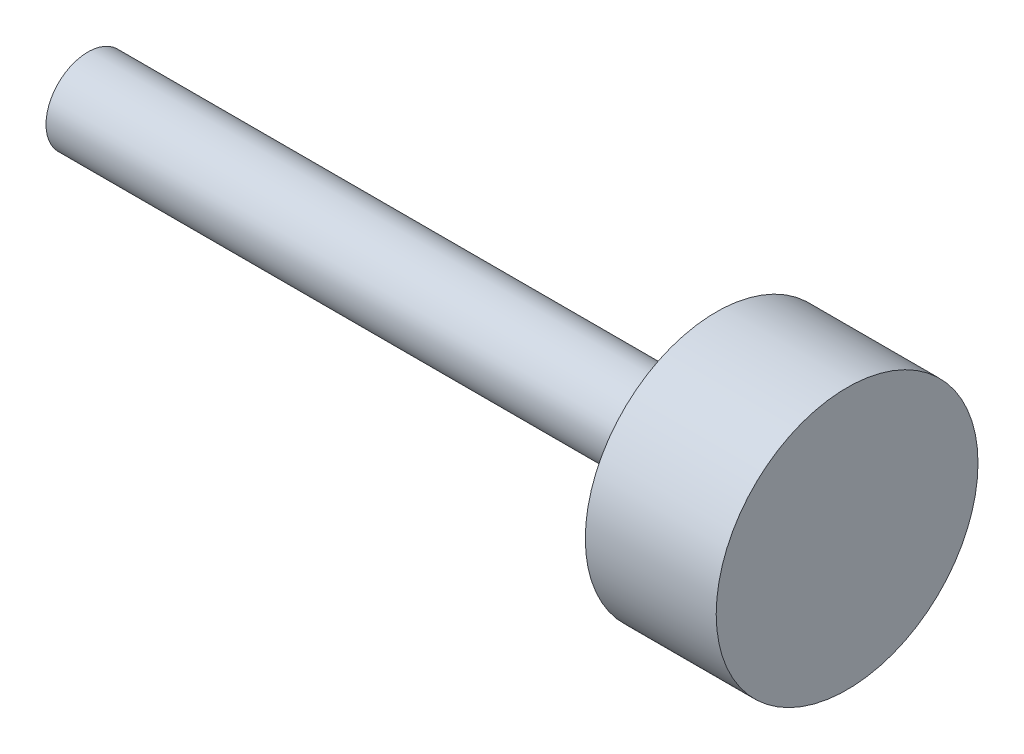
SolidWorks part; units mm, degrees
ref_plane "Front Plane" through (0, 0, 0) normal (0, 0, 1) x (1, 0, 0)
ref_plane "Top Plane" through (0, 0, 0) normal (0, 1, 0) x (1, 0, 0)
ref_plane "Right Plane" through (0, 0, 0) normal (1, 0, 0) x (0, 0, -1)
sketch "Sketch1" plane through (0, 0, 0) normal (0, 0, 1) x (1, 0, 0)
  line L0 (0, 0) -> (9.2075, 0)
  line L1 (9.2075, 0) -> (9.2075, 1.5875)
  line L2 (9.2075, 1.5875) -> (7.62, 1.5875)
  line L3 (7.62, 1.5875) -> (7.62, 0.508)
  line L4 (7.62, 0.508) -> (0, 0.508)
  line L5 (0, 0.508) -> (0, 0)
  dimension "D1" = 7.62
  dimension "D2" = 1.5875
  dimension "D3" = 0.508
  dimension "D4" = 1.5875
revolve "Revolve1" add sketch "Sketch1" angle 360 about L0
